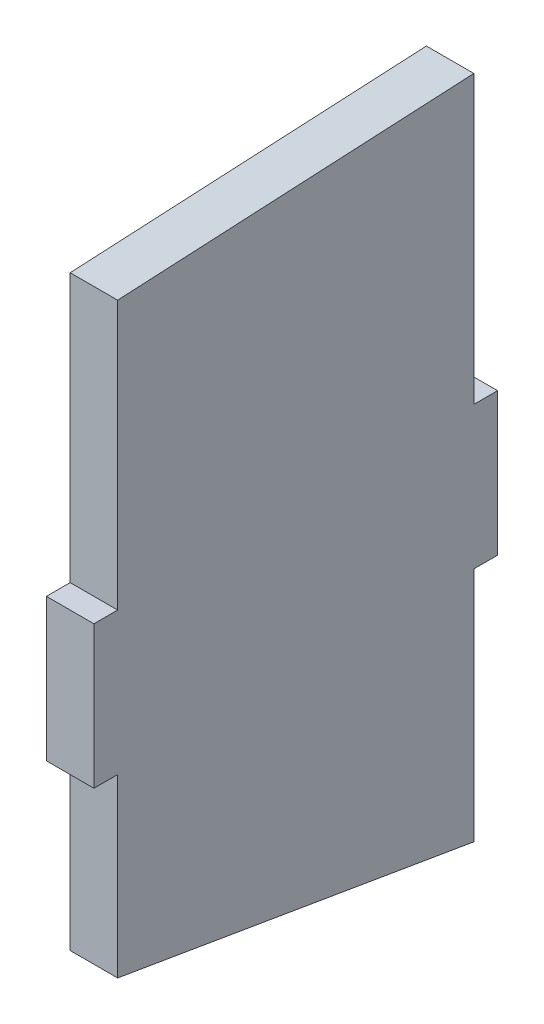
SolidWorks part; units mm, degrees
material "Pink Foam"
ref_plane "Front Plane" through (0, 0, 0) normal (0, 0, 1) x (1, 0, 0)
ref_plane "Top Plane" through (0, 0, 0) normal (0, 1, 0) x (1, 0, 0)
ref_plane "Right Plane" through (0, 0, 0) normal (1, 0, 0) x (0, 0, -1)
sketch "Sketch1" plane through (0, 0, 0) normal (1, 0, 0) x (0, 0, -1)
  line L0 (-95.25, 181.6249) -> (95.25, 191.3875)
  line L1 (-95.25, -203.2) -> (95.25, -203.2)
  line L2 (-95.25, -203.2) -> (-95.25, 203.2)
  line L3 (-95.25, 203.2) -> (95.25, 203.2)
  line L4 (95.25, -203.2) -> (95.25, 203.2)
  line L5 (-95.25, -203.2) -> (95.25, 203.2) construction
  line L6 (-95.25, 203.2) -> (95.25, -203.2) construction
  line L7 (-107.95, -38.1) -> (107.95, -38.1)
  line L8 (-107.95, -38.1) -> (-107.95, 38.1)
  line L9 (-107.95, 38.1) -> (107.95, 38.1)
  line L10 (107.95, -38.1) -> (107.95, 38.1)
  line L11 (-107.95, -38.1) -> (107.95, 38.1) construction
  line L12 (-107.95, 38.1) -> (107.95, -38.1) construction
  line L14 (-95.25, -132.3207) -> (95.25, -164.5088)
  point P0 (0, 0)
  point P6 (0, 0)
  dimension "D1" = 190.5
  dimension "D2" = 215.9
  dimension "D3" = 76.2
  dimension "D4" = 406.4
  dimension "D5" = 21.5751
  dimension "D6" = 11.8125
  dimension "D7" = 38.6912
  dimension "D8" = 313.9456
extrude "Boss-Extrude1" add sketch "Sketch1" along normal blind 25.4 contours L2 L9 L4 L0 | L7 L10 L9 L4 | L9 L2 L7 L4 | L9 L8 L7 L2 | L2 L14 L4 L7
